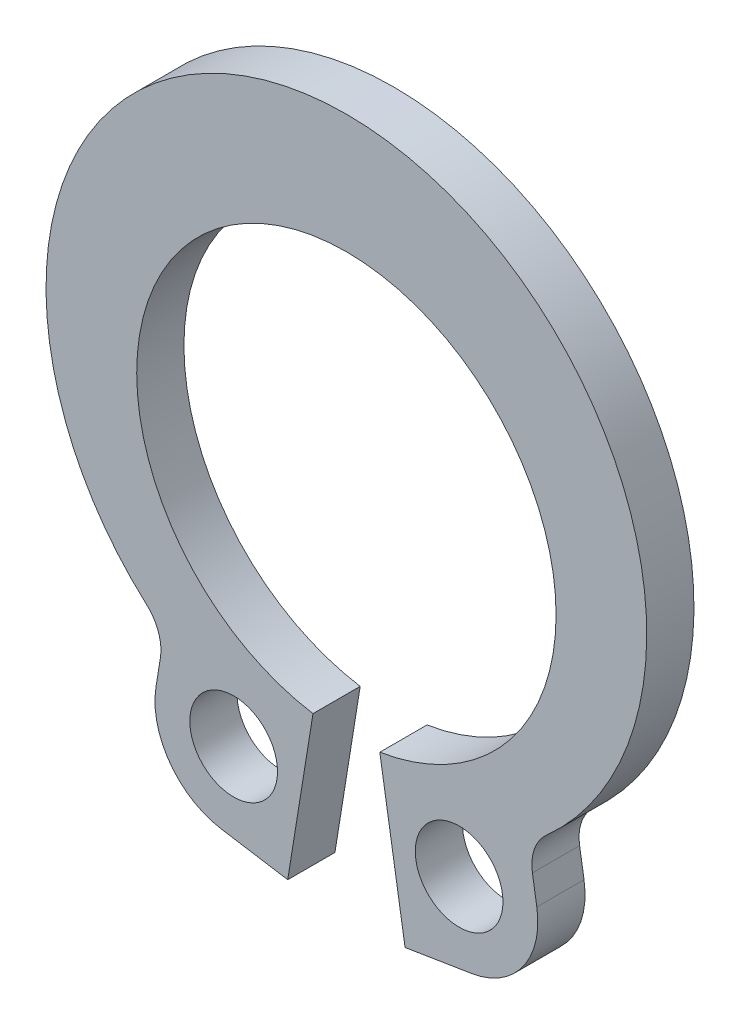
SolidWorks part; units mm, degrees
material "Aço cromo inoxidável"
ref_plane "Plane1" through (0, 0, 0) normal (0, 0, 1) x (1, 0, 0)
ref_plane "Plane2" through (0, 0, 0) normal (0, 1, 0) x (1, 0, 0)
ref_plane "Plane3" through (0, 0, 0) normal (1, 0, 0) x (0, 0, -1)
sketch "Clipboard" plane through (0, 0, 0) normal (0, 0, 1) x (1, 0, 0)
  line L0 (0, 0) -> (1.7272, 0)
  line L1 (0, 0) -> (0, 15.748)
  line L2 (0, 0) -> (0, -3.5814)
  line L3 (0, 0) -> (-2.54, 0)
  circle A0 centre (0, 0) radius 0.9906
  circle A1 centre (0, 0) radius 4.7371
  circle A2 centre (0, 0) radius 4.4958
  dimension "HoleDia" = 1.9812
  dimension "ShaftDia" = 9.4742
  dimension "FreeDia" = 8.9916
  dimension "LargeSection" = 1.7272
  dimension "RingHeight" = 15.748
  dimension "LugSection" = 3.5814
  dimension "LugBasis" = 2.54
sketch "BodySke" plane through (0, 0, 0) normal (0, 0, 1) x (1, 0, 0)
  line L0 (-1.5431, 0) -> (1.5431, 0) construction
  line L1 (0, 0) -> (0, 7.4295) construction
  line L2 (0.7548, -4.6766) -> (1.3255, -8.2122)
  line L3 (-0.7548, -4.6766) -> (-1.3255, -8.2122)
  line L4 (0, 0) -> (4.4654, -4.4654) construction
  line L5 (0, 0) -> (-4.4654, -4.4654) construction
  line L6 (1.3255, -8.2122) -> (2.83, -7.9694)
  line L7 (-1.3255, -8.2122) -> (-2.83, -7.9694)
  line L9 (4.2024, -5.3135) -> (4.302, -5.9308)
  line L14 (-4.2024, -5.3135) -> (-4.302, -5.9308)
  circle A0 centre (0, 0) radius 4.7371 construction
  arc A1 (0.7548, -4.6766) -> (-0.7548, -4.6766) centre (0, 0) ccw
  arc A2 (4.4654, -4.4654) -> (-4.4654, -4.4654) centre (0, 0.6439) ccw construction
  arc A3 (-4.302, -5.9308) -> (-2.83, -7.9694) centre (-2.5467, -6.2141) ccw
  arc A4 (-4.2024, -5.3135) -> (-4.5204, -4.4169) centre (-5.1803, -5.1556) ccw
  arc A5 (4.5204, -4.4169) -> (4.2024, -5.3135) centre (5.1803, -5.1556) ccw
  arc A6 (2.83, -7.9694) -> (4.302, -5.9308) centre (2.5467, -6.2141) ccw
  arc A7 (4.5204, -4.4169) -> (-4.5204, -4.4169) centre (0, 0.6439) ccw
  dimension "GrooveDia" = 9.4742
  dimension "D2" = 90
  dimension "LugFilletRad" = 1.778
  dimension "BodyFilletRad" = 0.9906
  dimension "LargeRad" = 7.4295
  dimension "SmallRad" = 6.3151
  dimension "LugY" = 8.3185
  dimension "GapAng" = 18.338
  dimension "LugWidth" = 3.302
extrude "Body" add sketch "BodySke" against normal blind 1.0668
sketch "HolSke" plane through (0, 0, 0) normal (0, 0, 1) x (1, 0, 0)
  line L0 (0, 0) -> (0, -2.9285) construction
  line L1 (1.3255, -8.2122) -> (2.83, -7.9694) construction
  line L2 (0.7548, -4.6766) -> (1.3255, -8.2122) construction
  circle A0 centre (2.5467, -6.2141) radius 0.9906
  circle A1 centre (-2.5467, -6.2141) radius 0.9906
  dimension "HoleDia" = 1.9812
  dimension "HoleInset" = 1.778
  dimension "HoleOffset" = 1.524
extrude "Holes" cut sketch "HolSke" against normal through all
sketch "NotSke" plane through (0, 0, 0) normal (0, 0, 1) x (1, 0, 0)
  line L2 (0, 0) -> (0, -3.0231) construction
  arc A0 (1.1409, -7.4313) -> (0.8403, -5.4731) centre (0.9906, -6.4522) ccw
  arc A1 (-0.8403, -5.4731) -> (-1.1409, -7.4313) centre (-0.9906, -6.4522) ccw
  arc A2 (-1.9555, -6.228) -> (1.9555, -6.228) centre (0, 0) ccw construction
  arc A3 (0.7548, -4.6766) -> (-0.7548, -4.6766) centre (0, 0) ccw construction
  circle A4 centre (0.9906, -6.4522) radius 0.9906 construction
  circle A5 centre (-0.9906, -6.4522) radius 0.9906 construction
  arc A6 (-0.8403, -5.4731) -> (0.8403, -5.4731) centre (0, 0) ccw
  arc A7 (-1.1409, -7.4313) -> (1.1409, -7.4313) centre (0, 0) ccw
  dimension "HoleDia" = 1.9812
  dimension "NotchRad" = 6.5278
extrude "Notch" [suppressed] cut sketch "NotSke" against normal through all
fillet "NotchFillets" [suppressed] radius 0.3903
equation "' \"ShaftDia@Clipboard\" = 0.058"
equation "' \"FreeDia@Clipboard\" = 0.055"
equation "' \"Thickness@Body\" = 0.015"
equation "' \"GrooveDia@BodySke\" = 0.058"
equation "' \"LugSection@Clipboard\" = 0.066"
equation "' \"RingHeight@Clipboard\" = 0.145"
equation "' \"HoleDia@Clipboard\" = 0.035"
equation "' \"LugBasis@Clipboard\" = 0.03"
equation "' \"ShaftDia@Clipboard\" = 0.092"
equation "' \"FreeDia@Clipboard\" = 0.089"
equation "' \"Thickness@Body\" = 0.025"
equation "' \"GrooveDia@BodySke\" = 0.092"
equation "' \"LugSection@Clipboard\" = 0.074"
equation "' \"RingHeight@Clipboard\" = 0.207"
equation "' \"HoleDia@Clipboard\" = 0.034"
equation "' \"LugBasis@Clipboard\" = 0.04"
equation "\"LargeRad@BodySke\" =  \"RingHeight@Clipboard\" - \"GrooveDia@BodySke\" / 2  - \"LugSection@Clipboard\""
equation "\"SmallRad@BodySke\" = \"LargeRad@BodySke\" * 0.85"
equation "\"LugY@BodySke\" =  \"GrooveDia@BodySke\" / 2 +  \"LugSection@Clipboard\" "
equation "\"GapAng@BodySke\" = 360 - 360 * (\"FreeDia@Clipboard\" /  \"GrooveDia@BodySke\" )"
equation "\"HoleDia@NotSke\" = \"HoleDia@Clipboard\""
equation "\"NotchRad@NotSke\" = \"LugY@BodySke\" - \"LugSection@Clipboard\" / 2"
equation "\"Radius@NotchFillets\" = (\"LugSection@Clipboard\" - \"HoleDia@Clipboard\" ) / 4.1"
equation "\"LugWidth@BodySke\" = \"LugBasis@Clipboard\"  * 1.3"
equation "\"LugFilletRad@BodySke\" = \"LugBasis@Clipboard\"  * 0.7"
equation "\"BodyFilletRad@BodySke\" = \"HoleDia@Clipboard\" / 2"
equation "\"HoleOffset@HolSke\" =  \"LugBasis@Clipboard\"  * 0.6"
equation "\"HoleInset@HolSke\" = \"LugBasis@Clipboard\"  * 0.7"
equation "\"HoleDia@HolSke\" = \"HoleDia@Clipboard\""
